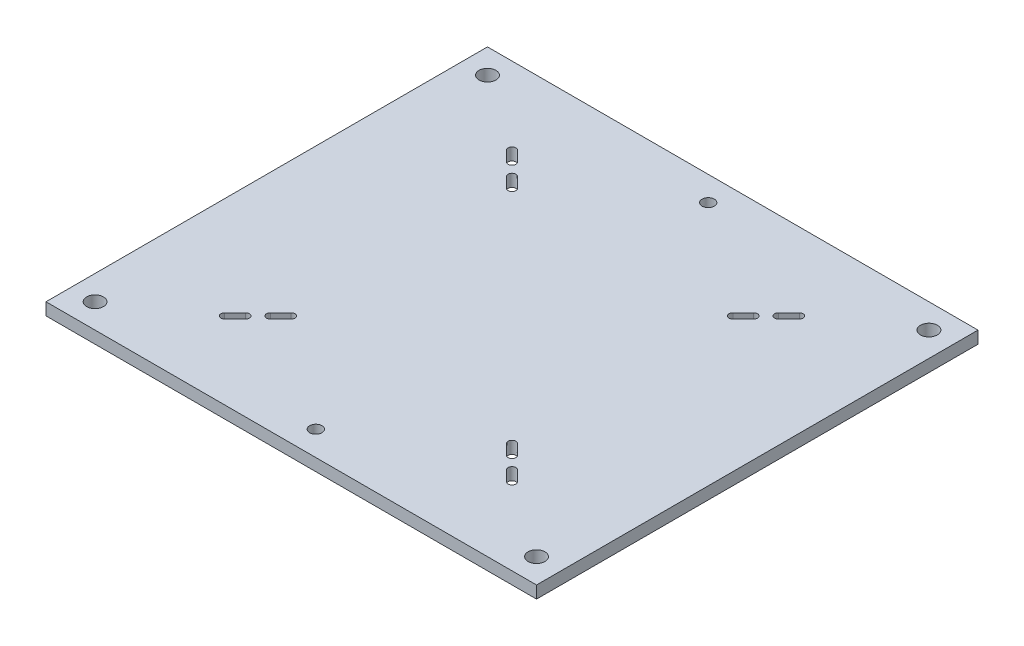
SolidWorks part; units mm, degrees
ref_plane "Front Plane" through (0, 0, 0) normal (0, 0, 1) x (1, 0, 0)
ref_plane "Top Plane" through (0, 0, 0) normal (0, 1, 0) x (1, 0, 0)
ref_plane "Right Plane" through (0, 0, 0) normal (1, 0, 0) x (0, 0, -1)
sketch "Sketch1" plane through (0, 0, 0) normal (0, 1, 0) x (1, 0, 0)
  line L1 (0, 0) -> (254, 0)
  line L2 (0, 0) -> (0, -228.6)
  line L3 (0, -228.6) -> (254, -228.6)
  line L4 (254, 0) -> (254, -228.6)
  dimension "D1" = 254
  dimension "D2" = 228.6
extrude "base plate" add sketch "Sketch1" against normal blind 6.35
sketch "center lines" plane through (0, 0, 0) normal (0, 1, 0) x (1, 0, 0)
  line L0 (127, 0) -> (127, -228.6) construction
  line L1 (254, 0) -> (0, 0) construction
  line L2 (0, -228.6) -> (254, -228.6) construction
  line L3 (0, -114.3) -> (254, -114.3) construction
  line L4 (0, 0) -> (0, -228.6) construction
  line L5 (254, -228.6) -> (254, 0) construction
sketch "Sketch3" plane through (0, 0, 0) normal (0, 1, 0) x (1, 0, 0)
  line L0 (42.875, -187.6487) -> (53.6513, -198.425)
  line L1 (53.6513, -198.425) -> (87.7763, -164.3)
  line L2 (87.7763, -164.3) -> (77, -153.5237)
  line L3 (77, -153.5237) -> (42.875, -187.6487)
  line L4 (52.619, -188.681) -> (58.0071, -183.2929) construction
  line L5 (51.2047, -187.2668) -> (56.5929, -181.8787)
  line L6 (54.0332, -190.0953) -> (59.4213, -184.7071)
  line L7 (0, -228.6) -> (254, -228.6) construction
  line L8 (69.8158, -171.4842) -> (64.4276, -176.8724) construction
  line L9 (71.23, -172.8984) -> (65.8419, -178.2866)
  line L10 (127, 0) -> (127, -228.6) construction
  line L11 (0, -114.3) -> (254, -114.3) construction
  line L12 (87.7763, -64.3) -> (77, -75.0763)
  line L13 (53.6513, -30.175) -> (87.7763, -64.3)
  line L14 (42.875, -40.9513) -> (53.6513, -30.175)
  line L15 (77, -75.0763) -> (42.875, -40.9513)
  line L16 (200.3487, -30.175) -> (166.2237, -64.3)
  line L17 (211.125, -40.9513) -> (200.3487, -30.175)
  line L18 (177, -75.0763) -> (211.125, -40.9513)
  line L19 (166.2237, -64.3) -> (177, -75.0763)
  line L20 (166.2237, -164.3) -> (177, -153.5237)
  line L21 (200.3487, -198.425) -> (166.2237, -164.3)
  line L22 (211.125, -187.6487) -> (200.3487, -198.425)
  line L23 (177, -153.5237) -> (211.125, -187.6487)
  line L24 (68.4016, -170.07) -> (63.0134, -175.4581)
  line L25 (52.619, -39.919) -> (58.0071, -45.3071) construction
  line L26 (51.2047, -41.3332) -> (56.5929, -46.7213)
  line L27 (54.0332, -38.5047) -> (59.4213, -43.8929)
  line L28 (69.8158, -57.1158) -> (64.4276, -51.7276) construction
  line L29 (71.23, -55.7016) -> (65.8419, -50.3134)
  line L30 (68.4016, -58.53) -> (63.0134, -53.1419)
  line L31 (201.381, -39.919) -> (195.9929, -45.3071) construction
  line L32 (202.7953, -41.3332) -> (197.4071, -46.7213)
  line L33 (199.9668, -38.5047) -> (194.5787, -43.8929)
  line L34 (184.1842, -57.1158) -> (189.5724, -51.7276) construction
  line L35 (182.77, -55.7016) -> (188.1581, -50.3134)
  line L36 (185.5984, -58.53) -> (190.9866, -53.1419)
  line L37 (184.1842, -171.4842) -> (189.5724, -176.8724) construction
  line L38 (182.77, -172.8984) -> (188.1581, -178.2866)
  line L39 (185.5984, -170.07) -> (190.9866, -175.4581)
  line L40 (201.381, -188.681) -> (195.9929, -183.2929) construction
  line L41 (202.7953, -187.2668) -> (197.4071, -181.8787)
  line L42 (199.9668, -190.0953) -> (194.5787, -184.7071)
  line L43 (77, -164.3) -> (77, -153.5237)
  line L44 (87.7763, -164.3) -> (77, -164.3)
  line L45 (77, -64.3) -> (77, -75.0763)
  line L46 (87.7763, -64.3) -> (77, -64.3)
  line L47 (177, -64.3) -> (177, -75.0763)
  line L48 (166.2237, -64.3) -> (177, -64.3)
  line L49 (177, -164.3) -> (177, -153.5237)
  line L50 (166.2237, -164.3) -> (177, -164.3)
  arc A0 (51.2047, -187.2668) -> (54.0332, -190.0953) centre (52.619, -188.681) ccw
  arc A1 (59.4213, -184.7071) -> (56.5929, -181.8787) centre (58.0071, -183.2929) ccw
  arc A2 (71.23, -172.8984) -> (68.4016, -170.07) centre (69.8158, -171.4842) ccw
  arc A3 (63.0134, -175.4581) -> (65.8419, -178.2866) centre (64.4276, -176.8724) ccw
  arc A4 (51.2047, -41.3332) -> (54.0332, -38.5047) centre (52.619, -39.919) cw
  arc A5 (59.4213, -43.8929) -> (56.5929, -46.7213) centre (58.0071, -45.3071) cw
  arc A6 (71.23, -55.7016) -> (68.4016, -58.53) centre (69.8158, -57.1158) cw
  arc A7 (63.0134, -53.1419) -> (65.8419, -50.3134) centre (64.4276, -51.7276) cw
  arc A8 (202.7953, -41.3332) -> (199.9668, -38.5047) centre (201.381, -39.919) ccw
  arc A9 (194.5787, -43.8929) -> (197.4071, -46.7213) centre (195.9929, -45.3071) ccw
  arc A10 (182.77, -55.7016) -> (185.5984, -58.53) centre (184.1842, -57.1158) ccw
  arc A11 (190.9866, -53.1419) -> (188.1581, -50.3134) centre (189.5724, -51.7276) ccw
  arc A12 (182.77, -172.8984) -> (185.5984, -170.07) centre (184.1842, -171.4842) cw
  arc A13 (190.9866, -175.4581) -> (188.1581, -178.2866) centre (189.5724, -176.8724) cw
  arc A14 (202.7953, -187.2668) -> (199.9668, -190.0953) centre (201.381, -188.681) cw
  arc A15 (194.5787, -184.7071) -> (197.4071, -181.8787) centre (195.9929, -183.2929) cw
  point P29 (55.313, -185.987)
  point P36 (67.1217, -174.1783)
  point P44 (55.313, -42.613)
  point P51 (67.1217, -54.4217)
  point P58 (198.687, -42.613)
  point P65 (186.8783, -54.4217)
  point P72 (186.8783, -174.1783)
  point P79 (198.687, -185.987)
  point P84 (59.4213, -181.8787)
  point P85 (63.0134, -178.2866)
  dimension "D6" = 2
  dimension "D10" = 5.08
  dimension "D9" = 10.16
  dimension "D1" = 48.26
  dimension "D2" = 15.24
  dimension "D3" = 45
  dimension "D4" = 100
  dimension "D5" = 100
  dimension "D7" = 7.62
  dimension "D8" = 7.62
extrude "slots" cut sketch "Sketch3" against normal through all contours A5 L27 A4 L26 | L33 A9 L32 A8 | L36 A11 L35 A10 | A13 L39 A12 L38 | A15 L42 A14 L41 | L6 A1 L5 A0 | L24 A3 L9 A2 | L30 A7 L29 A6
hole_wizard "Feet connection hole" positions "Sketch6" profile "Sketch7" hole size "1/4-20" standard "PEM® Inch" end condition through all
sketch "Sketch6" plane through (0, 0, 0) normal (0, 1, 0) x (1, 0, 0)
  line L0 (0, -228.6) -> (254, -228.6) construction
  line L1 (0, 0) -> (0, -228.6) construction
  line L2 (254, -228.6) -> (254, 0) construction
  line L3 (254, 0) -> (0, 0) construction
  point P3 (12.7, -215.9)
  point P19 (241.3, -12.7)
  point P33 (12.7, -12.7)
  point P37 (241.3, -215.9)
  dimension "D1" = 12.7
  dimension "D2" = 12.7
  dimension "D3" = 12.7
  dimension "D4" = 12.7
sketch "Sketch7" plane through (12.7, 0, 215.9) normal (1, 0, 0) x (0, 0, 1)
  line L0 (0, 0) -> (0, 6.35)
  line L1 (0, 6.35) -> (4.3688, 6.35)
  line L2 (4.3688, 6.35) -> (4.3688, 0)
  line L5 (4.3688, 0) -> (0, 0)
  line L11 (0, -6.35) -> (0, 107.95) construction
  dimension "Thru Hole Dia." = 8.7376
  dimension "Thru Hole Depth" = 6.35
hole_wizard "Hole for #10 Blind Fasteners (B,BS)1" positions "Sketch17" profile "Sketch18" hole size "#10-32" standard "PEM® Inch" end condition through all
sketch "Sketch17" plane through (0, 0, 0) normal (0, 1, 0) x (1, 0, 0)
  line L0 (0, -228.6) -> (254, -228.6) construction
  line L1 (254, 0) -> (0, 0) construction
  line L2 (254, -228.6) -> (254, 0) construction
  line L3 (0, 0) -> (0, -228.6) construction
  point P0 (127, -215.9)
  point P2 (127, -12.7)
  dimension "D1" = 12.7
  dimension "D2" = 12.7
  dimension "D3" = 127
  dimension "D4" = 127
sketch "Sketch18" plane through (127, 0, 215.9) normal (1, 0, 0) x (0, 0, 1)
  line L0 (0, 0) -> (0, 6.35)
  line L1 (0, 6.35) -> (3.175, 6.35)
  line L2 (3.175, 6.35) -> (3.175, 0)
  line L5 (3.175, 0) -> (0, 0)
  line L11 (0, -6.35) -> (0, 107.95) construction
  dimension "Thru Hole Dia." = 6.35
  dimension "Thru Hole Depth" = 6.35
